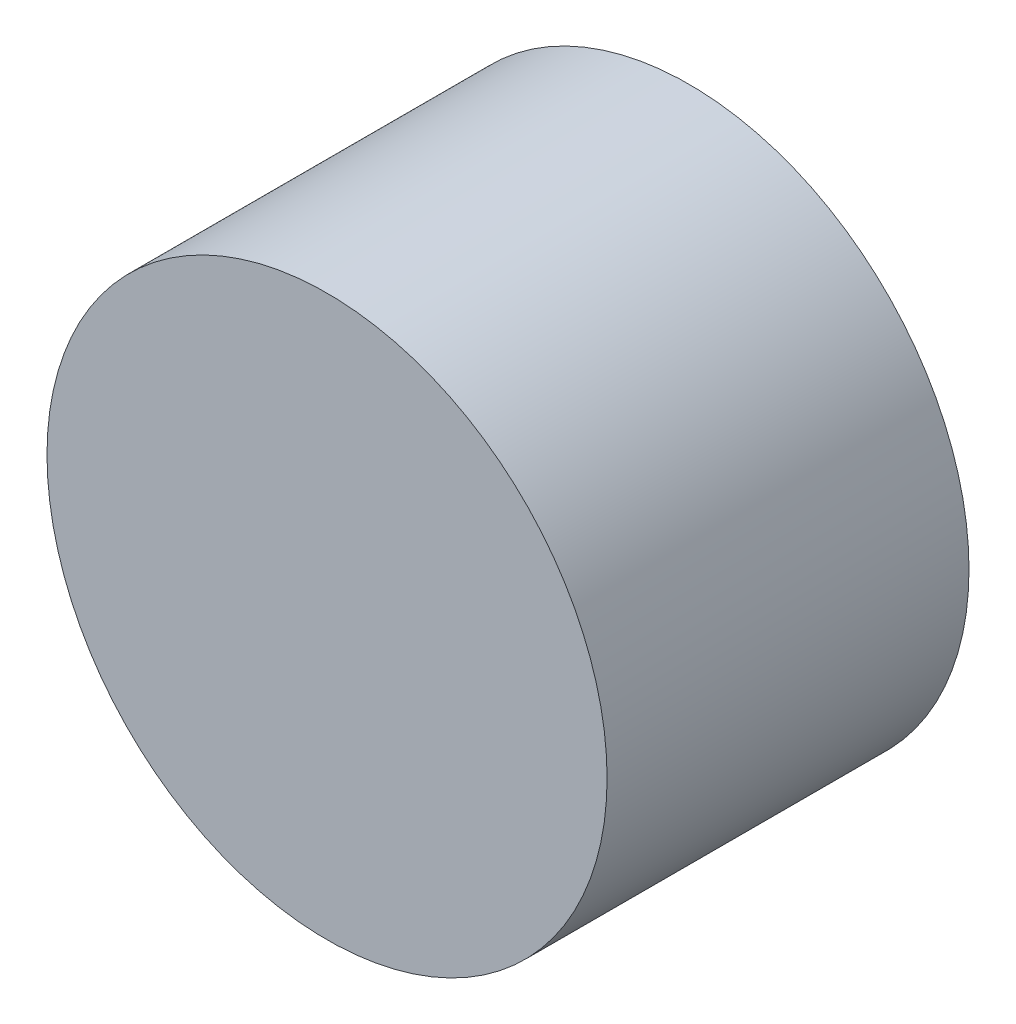
SolidWorks part; units mm, degrees
ref_plane "Front Plane" through (0, 0, 0) normal (0, 0, 1) x (1, 0, 0)
ref_plane "Top Plane" through (0, 0, 0) normal (0, 1, 0) x (1, 0, 0)
ref_plane "Right Plane" through (0, 0, 0) normal (1, 0, 0) x (0, 0, -1)
sketch "Sketch1" plane through (0, 0, 0) normal (0, 0, 1) x (1, 0, 0)
  circle A0 centre (0, 0) radius 32.5
  dimension "D1" = 65
extrude "Boss-Extrude1" add sketch "Sketch1" along normal blind 42
cosmetic thread "Cosmetic Thread1" parameters "D1"=25, "D2"=59.61
